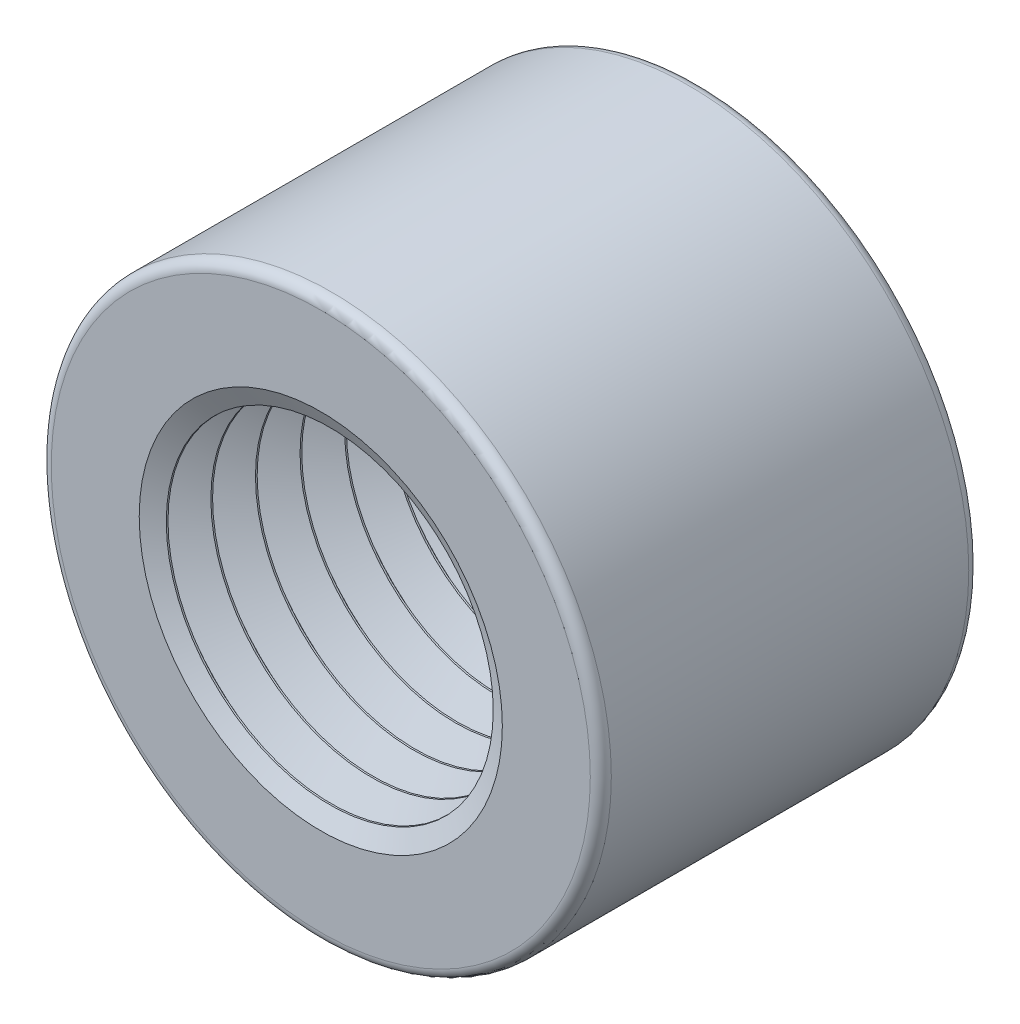
SolidWorks part; units mm, degrees
ref_plane "Front" through (0, 0, 0) normal (0, 0, 1) x (1, 0, 0)
ref_plane "Top" through (0, 0, 0) normal (0, 1, 0) x (1, 0, 0)
ref_plane "Right" through (0, 0, 0) normal (1, 0, 0) x (0, 0, -1)
sketch "Sketch1" plane through (0, 0, 0) normal (0, 0, 1) x (1, 0, 0)
  circle A0 centre (0, 0) radius 9.398
  dimension "OD" = 18.796
extrude "Extrude1" add sketch "Sketch1" along normal mid plane 12.7
sketch "Sketch5" plane through (0, 0, 0) normal (1, 0, 0) x (0, 0, -1)
  line L0 (-6.35, 4.8694) -> (6.35, 4.8694)
  line L1 (6.35, -9.398) -> (6.35, 9.398) construction
  line L2 (-6.35, 9.398) -> (-6.35, -9.398) construction
  line L3 (6.35, 4.8694) -> (6.35, 0)
  line L6 (0, 0) -> (2.43, 0) construction
  line L7 (6.35, 0) -> (-6.35, 0)
  line L10 (-6.35, 0) -> (-6.35, 4.8694)
  dimension "D1" = 4.8694
revolve "Cut-Revolve7" cut sketch "Sketch5" angle 360 about L6
fillet "Fillet1" radius 0.3528 2 edges at (9.398, 0, -6.35) (9.398, 0, 6.35)
sketch "Sketch2" plane through (0, 0, 0) normal (1, 0, 0) x (0, 0, -1)
  line L0 (97.9741, 0) -> (-104.2683, 0) construction
  line L1 (-123.0041, 13.369) -> (283.3943, -12.057) construction
  line L2 (-6.35, 9.398) -> (-6.35, -9.398) construction
  line L3 (-6.35, 5.5051) -> (83.3781, -0.1087) construction
  line L5 (83.3781, 1.0224) -> (-23.5825, 7.7143) construction
  line L6 (-22.1204, 7.6228) -> (-21.5404, 6.4554)
  line L7 (-23.5825, 7.7143) -> (-23.5288, 7.7109)
  line L8 (-23.5288, 7.7109) -> (-22.9488, 6.5435)
  line L9 (-22.9488, 6.5435) -> (-22.8951, 6.5402)
  line L10 (-22.8951, 6.5402) -> (-22.1741, 7.6262)
  line L11 (-22.9219, 6.5419) -> (-23.6475, -5.0555) construction
  line L12 (-22.1741, 7.6262) -> (-22.1204, 7.6228)
  line L13 (-21.4867, 6.4521) -> (-20.7658, 7.5381)
  line L14 (-20.7658, 7.5381) -> (-20.7121, 7.5347)
  line L15 (-21.5404, 6.4554) -> (-21.4867, 6.4521)
  line L16 (-20.7121, 7.5347) -> (-20.1321, 6.3673)
  line L17 (-20.0784, 6.364) -> (-19.3574, 7.4499)
  line L18 (-19.3574, 7.4499) -> (-19.3037, 7.4466)
  line L19 (-20.1321, 6.3673) -> (-20.0784, 6.364)
  line L20 (-19.3037, 7.4466) -> (-18.7237, 6.2792)
  line L21 (-18.67, 6.2758) -> (-17.9491, 7.3618)
  line L22 (-17.9491, 7.3618) -> (-17.8954, 7.3585)
  line L23 (-18.7237, 6.2792) -> (-18.67, 6.2758)
  line L24 (-17.8954, 7.3585) -> (-17.3154, 6.1911)
  line L25 (-17.2617, 6.1877) -> (-16.5407, 7.2737)
  line L26 (-16.5407, 7.2737) -> (-16.487, 7.2704)
  line L27 (-17.3154, 6.1911) -> (-17.2617, 6.1877)
  line L28 (-16.487, 7.2704) -> (-15.907, 6.103)
  line L29 (-15.8533, 6.0996) -> (-15.1323, 7.1856)
  line L30 (-15.1323, 7.1856) -> (-15.0786, 7.1822)
  line L31 (-15.907, 6.103) -> (-15.8533, 6.0996)
  line L32 (-15.0786, 7.1822) -> (-14.4986, 6.0149)
  line L33 (-14.445, 6.0115) -> (-13.724, 7.0975)
  line L34 (-13.724, 7.0975) -> (-13.6703, 7.0941)
  line L35 (-14.4986, 6.0149) -> (-14.445, 6.0115)
  line L36 (-13.6703, 7.0941) -> (-13.0903, 5.9268)
  line L37 (-13.0366, 5.9234) -> (-12.3156, 7.0094)
  line L38 (-12.3156, 7.0094) -> (-12.2619, 7.006)
  line L39 (-13.0903, 5.9268) -> (-13.0366, 5.9234)
  line L40 (-12.2619, 7.006) -> (-11.6819, 5.8386)
  line L41 (-11.6282, 5.8353) -> (-10.9073, 6.9213)
  line L42 (-10.9073, 6.9213) -> (-10.8536, 6.9179)
  line L43 (-11.6819, 5.8386) -> (-11.6282, 5.8353)
  line L44 (-10.8536, 6.9179) -> (-10.2736, 5.7505)
  line L45 (-10.2199, 5.7472) -> (-9.4989, 6.8332)
  line L46 (-9.4989, 6.8332) -> (-9.4452, 6.8298)
  line L47 (-10.2736, 5.7505) -> (-10.2199, 5.7472)
  line L48 (-9.4452, 6.8298) -> (-8.8652, 5.6624)
  line L49 (-8.8115, 5.6591) -> (-8.0905, 6.745)
  line L50 (-8.0905, 6.745) -> (-8.0369, 6.7417)
  line L51 (-8.8652, 5.6624) -> (-8.8115, 5.6591)
  line L52 (-8.0369, 6.7417) -> (-7.4569, 5.5743)
  line L53 (-7.4032, 5.5709) -> (-6.6822, 6.6569)
  line L54 (-6.6822, 6.6569) -> (-6.6285, 6.6536)
  line L55 (-7.4569, 5.5743) -> (-7.4032, 5.5709)
  line L56 (-6.6285, 6.6536) -> (-6.0485, 5.4862)
  line L57 (-5.9948, 5.4828) -> (-5.2738, 6.5688)
  line L58 (-5.2738, 6.5688) -> (-5.2201, 6.5655)
  line L59 (-6.0485, 5.4862) -> (-5.9948, 5.4828)
  line L60 (-5.2201, 6.5655) -> (-4.6401, 5.3981)
  line L61 (-4.5865, 5.3947) -> (-3.8655, 6.4807)
  line L62 (-3.8655, 6.4807) -> (-3.8118, 6.4773)
  line L63 (-4.6401, 5.3981) -> (-4.5865, 5.3947)
  line L64 (-3.8118, 6.4773) -> (-3.2318, 5.31)
  line L65 (-3.1781, 5.3066) -> (-2.4571, 6.3926)
  line L66 (-2.4571, 6.3926) -> (-2.4034, 6.3892)
  line L67 (-3.2318, 5.31) -> (-3.1781, 5.3066)
  line L68 (-2.4034, 6.3892) -> (-1.8234, 5.2219)
  line L69 (-1.7697, 5.2185) -> (-1.0488, 6.3045)
  line L70 (-1.0488, 6.3045) -> (-0.9951, 6.3011)
  line L71 (-1.8234, 5.2219) -> (-1.7697, 5.2185)
  line L72 (-0.9951, 6.3011) -> (-0.4151, 5.1337)
  line L73 (-0.3614, 5.1304) -> (0.3596, 6.2164)
  line L74 (0.3596, 6.2164) -> (0.4133, 6.213)
  line L75 (-0.4151, 5.1337) -> (-0.3614, 5.1304)
  line L76 (0.4133, 6.213) -> (0.9933, 5.0456)
  line L77 (1.047, 5.0423) -> (1.768, 6.1283)
  line L78 (1.768, 6.1283) -> (1.8216, 6.1249)
  line L79 (0.9933, 5.0456) -> (1.047, 5.0423)
  line L80 (1.8216, 6.1249) -> (2.4016, 4.9575)
  line L81 (2.4553, 4.9542) -> (3.1763, 6.0401)
  line L82 (3.1763, 6.0401) -> (3.23, 6.0368)
  line L83 (2.4016, 4.9575) -> (2.4553, 4.9542)
  line L84 (3.23, 6.0368) -> (3.81, 4.8694)
  line L85 (4.5847, 5.952) -> (4.6384, 5.9487) [skipped]
  line L86 (3.81, 4.8694) -> (3.8637, 4.866) [skipped]
  line L87 (3.81, 4.8694) -> (3.81, 0)
  line L88 (3.8637, 4.866) -> (4.5847, 5.952) [skipped]
  line L89 (3.81, 0) -> (-23.5825, 0)
  line L90 (-23.5825, 7.7143) -> (-23.5825, 0)
  line L91 (46.2639, 6.0706) -> (-58.9639, 6.0706) construction
  point P21 (-23.2388, 7.1272)
  point P67 (-6.35, 6.0706)
  dimension "D1" = 3.58
  dimension "D4" = 60
  dimension "Height of Thread-h" = 1.1289
  dimension "Pitch" = 1.4111
  dimension "Depth" = 10.16
  dimension "Pitch Dia" = 6.0706
revolve "Cut-Revolve5" cut sketch "Sketch2" angle 360 about L0
equation "\"Height of Thread-h@Sketch2\" = \"Pitch@Sketch2\"*.8"
equation "\"D1@Fillet1\" = \"Pitch@Sketch2\"*.25"
